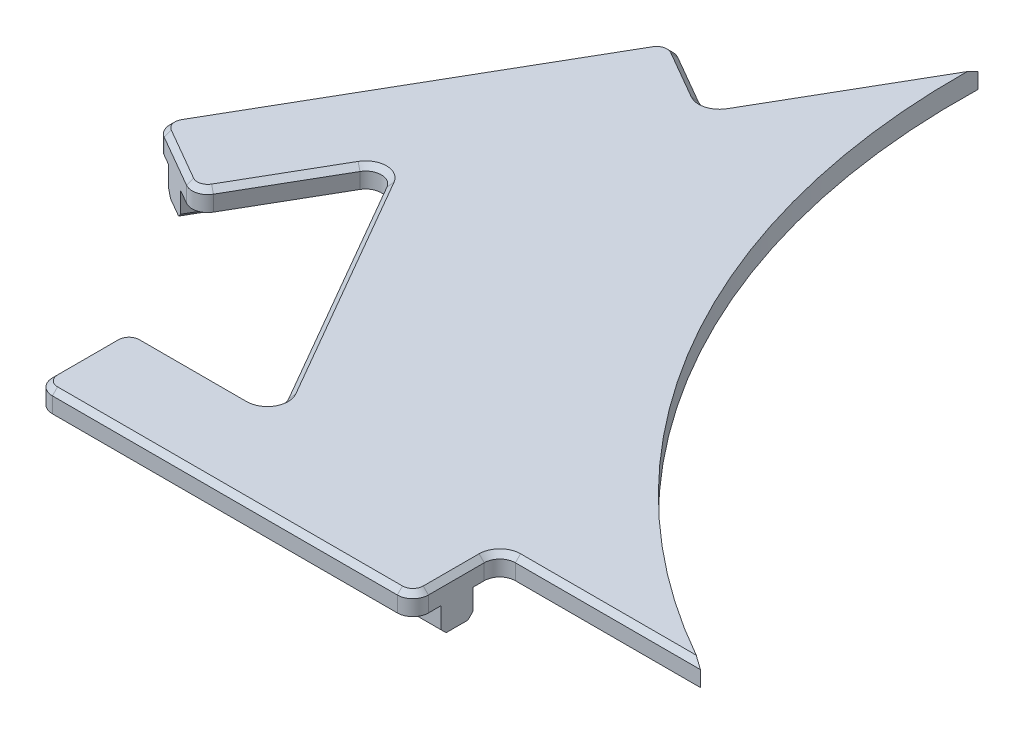
SolidWorks part; units mm, degrees
ref_plane "Front Plane" through (0, 0, 0) normal (0, 0, 1) x (1, 0, 0)
ref_plane "Top Plane" through (0, 0, 0) normal (0, 1, 0) x (1, 0, 0)
ref_plane "Right Plane" through (0, 0, 0) normal (1, 0, 0) x (0, 0, -1)
sketch "Sketch1" plane through (0, 0, 0) normal (0, 1, 0) x (1, 0, 0)
  line L9 (0, 0) -> (48, 0) construction
  line L10 (48, 0) -> (404, 0) construction
  line L11 (404, 0) -> (452, 0) construction
  line L12 (452, 0) -> (428, 41.5692) construction
  line L13 (428, 41.5692) -> (250, 349.8743) construction
  line L14 (250, 349.8743) -> (226, 391.4435) construction
  line L15 (226, 391.4435) -> (202, 349.8743) construction
  line L16 (202, 349.8743) -> (24, 41.5692) construction
  line L17 (24, 41.5692) -> (0, 0) construction
  line L18 (48, 0) -> (24, 41.5692) construction
  line L19 (202, 349.8743) -> (250, 349.8743) construction
  line L20 (428, 41.5692) -> (404, 0) construction
  line L22 (15.3397, 46.5692) -> (193.3397, 354.8743) construction
  line L28 (404, -10) -> (48, -10) construction
  line L30 (48, -10) -> (48, 10) construction
  line L31 (404, -10) -> (404, 10) construction
  line L32 (15.3397, 46.5692) -> (32.6603, 36.5692) construction
  line L33 (193.3397, 354.8743) -> (210.6603, 344.8743) construction
  line L34 (404, 10) -> (48, 10) construction
  line L35 (32.6603, 36.5692) -> (210.6603, 344.8743) construction
  line L45 (76, 10) -> (46.6603, 60.8179)
  line L51 (0, 0) -> (339, 195.7217) construction
  line L52 (76, 10) -> (76, 8.5)
  line L53 (76, 8.5) -> (48, 8.5)
  line L54 (48, 8.5) -> (48, -9.25)
  line L55 (48, -9.25) -> (120.45, -9.25)
  line L56 (120.45, -9.25) -> (120.45, 7.5)
  line L57 (120.45, 7.5) -> (159.0998, 7.5)
  line L58 (159.0998, 7.5) -> (86.0451, 134.0345)
  line L59 (52.2143, 108.9378) -> (66.7202, 100.5628)
  line L60 (66.7202, 100.5628) -> (86.0451, 134.0345)
  line L61 (46.6603, 60.8179) -> (45.3612, 61.5679)
  line L62 (45.3612, 61.5679) -> (31.3612, 37.3192)
  line L63 (31.3612, 37.3192) -> (15.9893, 46.1942)
  line L64 (15.9893, 46.1942) -> (52.2143, 108.9378)
  line L65 (226, 391.4435) -> (226, 0) construction
  line L66 (452, 0) -> (113, 195.7217) construction
  arc A0 (48, -10) -> (15.3397, 46.5692) centre (48, 27.7128) cw construction
  circle A3 centre (226, 130.4812) radius 140 construction
  point P32 (122.5725, 70.7672)
  point P33 (61.3301, 35.409)
  dimension "D7" = 72.45
  dimension "D10" = 280
  dimension "D1" = 356
  dimension "D2" = 48
  dimension "D3" = 10
  dimension "D4" = 28
  dimension "D5" = 1.5
  dimension "D6" = 1.5
  dimension "D8" = 17.5
extrude "Boss-Extrude1" add sketch "Sketch1" along normal blind 4
fillet "Fillet1" radius 3 8 edges at (66.7202, 2, -100.5628) (120.45, 2, -7.5) (52.2143, 2, -108.9378) (15.9893, 2, -46.1942) (48, 2, -8.5) (48, 2, 9.25) (120.45, 2, 9.25) (31.3612, 2, -37.3192)
sketch "Sketch2" plane through (0, 4, 0) normal (0, 1, 0) x (1, 0, 0)
  line L0 (46.6603, 60.8179) -> (45.7942, 62.3179)
  line L1 (45.7942, 62.3179) -> (45.3612, 61.5679)
  line L2 (45.3612, 61.5679) -> (46.6603, 60.8179)
  line L3 (76, 8.5) -> (76.866, 8.5)
  line L4 (76.866, 8.5) -> (76, 10)
  line L5 (76, 10) -> (76, 8.5)
  line L6 (76, 8.5) -> (51, 8.5) construction
  line L7 (46.6603, 60.8179) -> (76, 10) construction
  line L8 (32.8612, 39.9173) -> (45.3612, 61.5679) construction
extrude "Cut-Extrude1" cut sketch "Sketch2" against normal through all
fillet "Fillet4" radius 3 2 edges at (76.866, 2, -8.5) (45.7942, 2, -62.3179)
chamfer "Chamfer1" distance 1 angle 45 22 edges at (31.0396, 4, -38.5195) (23.6752, 4, -41.7567) (17.1896, 4, -46.5158) (34.1018, 4, -77.566) (52.5359, 4, -107.7375) (59.4672, 4, -104.7503) (66.3986, 4, -101.7631) (77.1326, 4, -118.5977) (122.5725, 4, -70.7672) (141.2749, 4, -7.5) (121.3287, 4, -6.6213) (120.45, 4, 0.875) (119.5713, 4, 8.3713) (84.225, 4, 9.25) (48.8787, 4, 8.3713) (48, 4, 0.375) (48.8787, 4, -7.6213) (61.3349, 4, -8.5) (74.2679, 4, -10) (61.3301, 4, -35.409) (45.7942, 4, -59.3179) (38.0287, 4, -48.8676)
sketch "Sketch3" plane through (0, 4, 0) normal (0, 1, 0) x (1, 0, 0)
  circle A0 centre (226, 130.4812) radius 140
  circle A1 centre (226, 130.4812) radius 140 construction
extrude "Cut-Extrude2" cut sketch "Sketch3" against normal through all
sketch "Sketch4" plane through (0, 0, 0) normal (0, -1, 0) x (1, 0, 0)
  line L0 (48, 0.75) -> (120.45, 0.75) construction
  line L1 (48, -5.5) -> (48, 6.25) construction
  line L2 (120.45, 6.25) -> (120.45, -4.5) construction
  line L3 (23.3505, -41.9442) -> (59.5755, -104.6878) construction
  line L4 (18.5873, -44.6942) -> (28.7631, -38.8192) construction
  line L5 (64.1221, -102.0628) -> (54.8123, -107.4378) construction
  line L6 (51, 9.25) -> (117.45, 9.25) construction
  line L7 (50.7143, -106.3397) -> (17.4893, -48.7923) construction
  line L8 (20.6658, -43.4942) -> (56.8908, -106.2378)
  line L9 (56.8908, -106.2378) -> (62.2602, -103.1378)
  line L10 (62.2602, -103.1378) -> (26.0352, -40.3942)
  line L12 (48, 0.75) -> (48, 3.85)
  line L13 (23.3505, -41.9442) -> (20.6658, -43.4942)
  line L14 (23.3505, -41.9442) -> (26.0352, -40.3942)
  line L15 (48, 3.85) -> (120.45, 3.85)
  line L16 (120.45, 3.85) -> (120.45, -2.35)
  line L17 (120.45, -2.35) -> (48, -2.35)
  line L18 (48, -2.35) -> (48, 0.75)
  dimension "D1" = 6.2
  dimension "D2" = 8.5
  dimension "D3" = 8.5
extrude "Boss-Extrude2" add sketch "Sketch4" along normal blind 5
chamfer "Chamfer2" distance 1 angle 45 4 edges at (38.7783, -5, -74.866) (44.1477, -5, -71.766) (84.225, -5, 3.85) (84.225, -5, -2.35)
